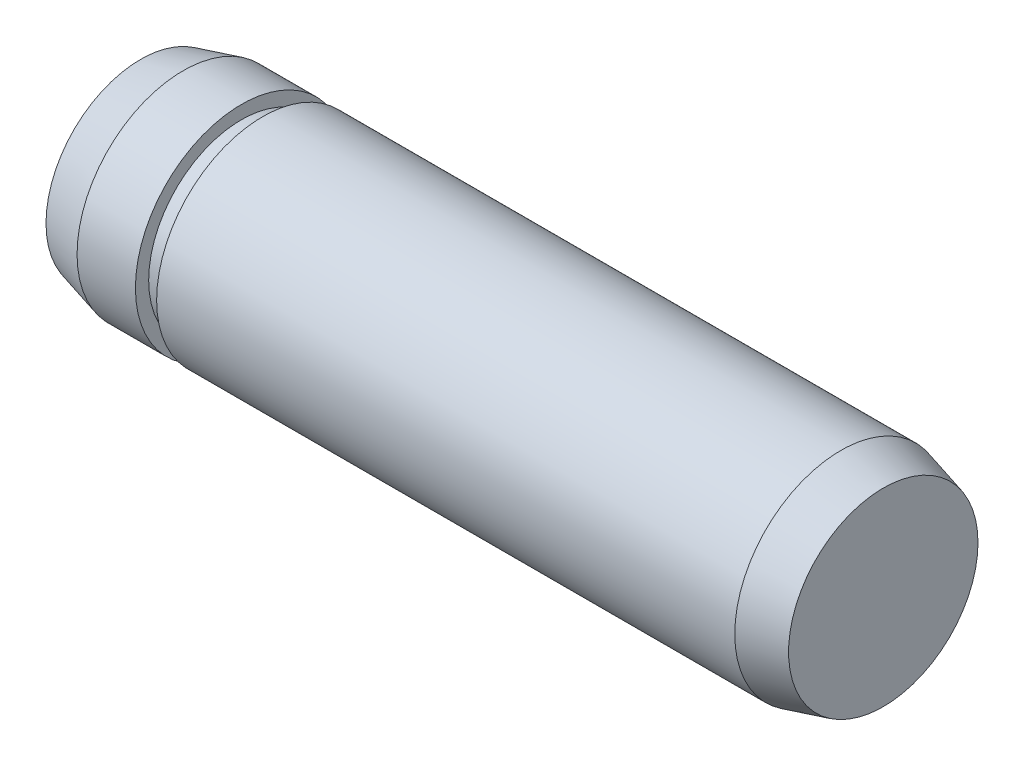
SolidWorks part; units mm, degrees
material "Cast Stainless Steel"
ref_plane "Front Plane" through (0, 0, 0) normal (0, 0, 1) x (1, 0, 0)
ref_plane "Top Plane" through (0, 0, 0) normal (0, 1, 0) x (1, 0, 0)
ref_plane "Right Plane" through (0, 0, 0) normal (1, 0, 0) x (0, 0, -1)
sketch "Sketch1" plane through (0, 0, 0) normal (0, 0, 1) x (1, 0, 0)
  line L0 (-12.4, 0) -> (12.4, 0) construction
  line L1 (12.4, 4) -> (12.4, -4) construction
  line L2 (-12.4, 4) -> (-12.4, -4) construction
  line L3 (14, 4) -> (14, -4) construction
  line L4 (-14, 4) -> (-14, -4) construction
  line L5 (-12.4, 0) -> (-14, 0) construction
  line L6 (12.4, 0) -> (14, 0) construction
  dimension "Dia" = 8
  dimension "C" = 1.6
  dimension "D1" = 1.6
  dimension "Length" = 28
sketch "Sketch2" plane through (0, 0, 0) normal (1, 0, 0) x (0, 0, -1)
  circle A0 centre (0, 0) radius 4
extrude "Extrude1" add sketch "Sketch2" against normal up to vertex (12.4 mm away) and the other way up to vertex (12.4 mm away) up to point (-12.4, 4, 0) other way up to point (12.4, 4, 0)
sketch "Sketch3" plane through (12.4, 0, 0) normal (1, 0, 0) x (0, 0, -1)
  circle A1 centre (0, 0) radius 4
  circle A2 centre (0, 0) radius 4
  dimension "D1" = 0
extrude "Extrude2" add sketch "Sketch3" along normal up to vertex (1.6 mm away) draft 15 up to point (14, 0, 0)
sketch "Sketch4" plane through (-12.4, 0, 0) normal (-1, 0, 0) x (0, 0, 1)
  circle A1 centre (0, 0) radius 4
  circle A2 centre (0, 0) radius 4
  dimension "D1" = 0
extrude "Extrude3" add sketch "Sketch4" along normal up to vertex (1.6 mm away) draft 15 up to point (-14, 0, 0)
ref_plane "Plane1" through (-9.4, 0, 0) normal (-1, 0, 0) x (0, 0, 1)
sketch "Sketch5" plane through (-9.4, 0, 0) normal (-1, 0, 0) x (0, 0, 1)
  circle A0 centre (0, 0) radius 3.5
  circle A1 centre (0, 0) radius 4
  dimension "D1" = 7
  dimension "D2" = 8
extrude "Cut-Extrude1" cut sketch "Sketch5" along normal blind 0.8
equation "\"D1@Sketch1\" = \"C@Sketch1\""
